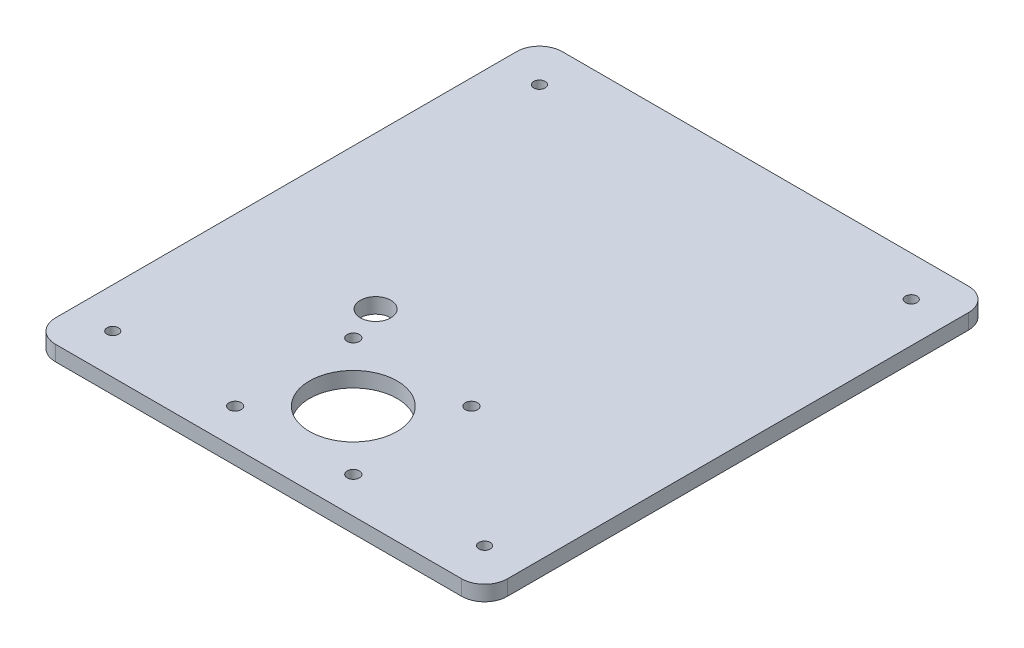
SolidWorks part; units mm, degrees
ref_plane "Front Plane" through (0, 0, 0) normal (0, 0, 1) x (1, 0, 0)
ref_plane "Top Plane" through (0, 0, 0) normal (0, 1, 0) x (1, 0, 0)
ref_plane "Right Plane" through (0, 0, 0) normal (1, 0, 0) x (0, 0, -1)
sketch "Sketch1" plane through (0, 57.3962, 0) normal (0, -1, 0) x (1, 0, 0)
  line L0 (117.078, 202.0764) -> (117.078, 81.0691) construction
  line L1 (4.4743, 208.0728) -> (111.0816, 208.0728) construction
  line L2 (-1.522, 81.0691) -> (-1.522, 202.0764) construction
  line L3 (111.0816, 75.0728) -> (4.4743, 75.0728) construction
  line L4 (117.078, 202.0764) -> (117.078, 81.0691)
  line L5 (4.4743, 208.0728) -> (111.0816, 208.0728)
  line L6 (-1.522, 81.0691) -> (-1.522, 202.0764)
  line L7 (111.0816, 75.0728) -> (4.4743, 75.0728)
  ellipse E0 centre (111.0743, 202.0691) end of major axis (115.3221, 206.3169) minor radius 6 (117.078, 202.0764) -> (111.0816, 208.0728) ccw construction
  ellipse E1 centre (4.4816, 202.0691) end of major axis (0.2338, 206.3169) minor radius 6 (4.4743, 208.0728) -> (-1.522, 202.0764) ccw construction
  ellipse E2 centre (4.4816, 81.0764) end of major axis (0.2338, 76.8286) minor radius 6 (-1.522, 81.0691) -> (4.4743, 75.0728) ccw construction
  ellipse E3 centre (111.0743, 81.0764) end of major axis (115.3221, 76.8286) minor radius 6 (111.0816, 75.0728) -> (117.078, 81.0691) ccw construction
  ellipse E4 centre (111.0743, 202.0691) end of major axis (115.3221, 206.3169) minor radius 6 (117.078, 202.0764) -> (111.0816, 208.0728) ccw
  ellipse E5 centre (4.4816, 202.0691) end of major axis (0.2338, 206.3169) minor radius 6 (4.4743, 208.0728) -> (-1.522, 202.0764) ccw
  ellipse E6 centre (4.4816, 81.0764) end of major axis (0.2338, 76.8286) minor radius 6 (-1.522, 81.0691) -> (4.4743, 75.0728) ccw
  ellipse E7 centre (111.0743, 81.0764) end of major axis (115.3221, 76.8286) minor radius 6 (111.0816, 75.0728) -> (117.078, 81.0691) ccw
extrude "Boss-Extrude1" add sketch "Sketch1" along normal blind 4
sketch "Sketch2" plane through (0, 53.3962, 0) normal (0, -1, 0) x (1, 0, 0)
  circle A0 centre (57.6312, 183.0715) radius 11.5
  circle A1 centre (73.1312, 198.5715) radius 1.6
  circle A2 centre (42.1312, 198.5715) radius 1.6
  circle A3 centre (42.1312, 167.5715) radius 1.6
  circle A4 centre (73.1312, 167.5715) radius 1.6
  dimension "D1" = 23
  dimension "D2" = 3.2
  dimension "D3" = 3.2
  dimension "D4" = 3.2
  dimension "D5" = 3.2
extrude "Cut-Extrude1" cut sketch "Sketch2" against normal up to next
sketch "Sketch4" plane through (0, 53.3962, 0) normal (0, -1, 0) x (1, 0, 0)
  circle A4 centre (8.9941, 197.5566) radius 1.5
  circle A5 centre (106.5619, 197.5566) radius 1.5
  circle A6 centre (8.9941, 85.5889) radius 1.5
  circle A7 centre (106.5619, 85.5889) radius 1.5
  dimension "D1" = 3
  dimension "D2" = 3
  dimension "D3" = 3
  dimension "D4" = 3
extrude "Cut-Extrude2" cut sketch "Sketch4" against normal up to next
sketch "Sketch5" plane through (0, 53.3962, 0) normal (0, -1, 0) x (1, 0, 0)
  line L0 (-1.522, 202.0764) -> (-1.522, 81.0691) construction
  line L1 (52.478, 163.0728) -> (62.478, 163.0728)
  line L2 (52.478, 163.0728) -> (52.478, 133.0728)
  line L3 (52.478, 133.0728) -> (62.478, 133.0728)
  line L4 (62.478, 163.0728) -> (62.478, 133.0728)
  line L5 (111.0816, 208.0728) -> (4.4743, 208.0728) construction
  dimension "D1" = 10
  dimension "D2" = 30
  dimension "D3" = 54
  dimension "D4" = 45
extrude "Boss-Extrude2" add sketch "Sketch5" along normal blind 12
fillet "Fillet1" radius 1.5 8 edges at (57.478, 53.3962, 163.0728) (62.478, 53.3962, 148.0728) (57.478, 53.3962, 133.0728) (52.478, 53.3962, 148.0728) (52.478, 47.3962, 163.0728) (62.478, 47.3962, 163.0728) (62.478, 47.3962, 133.0728) (52.478, 47.3962, 133.0728)
sketch "Sketch6" plane through (0, 53.3962, 0) normal (0, -1, 0) x (1, 0, 0)
  line L0 (111.0816, 208.0728) -> (4.4743, 208.0728) construction
  line L1 (-1.522, 202.0764) -> (-1.522, 81.0691) construction
  circle A0 centre (38.478, 158.0728) radius 4
  dimension "D1" = 8
  dimension "D2" = 50
  dimension "D3" = 40
extrude "Cut-Extrude3" cut sketch "Sketch6" against normal up to next
